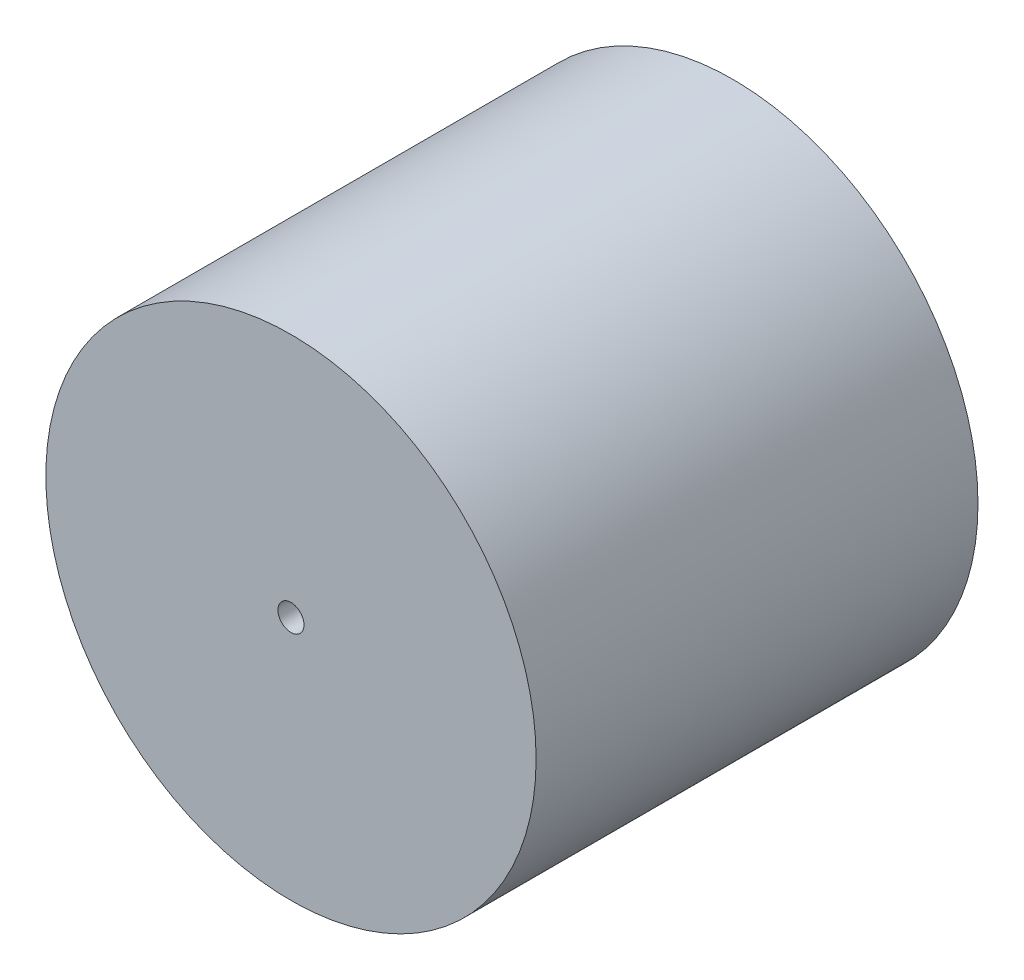
SolidWorks part; units mm, degrees
ref_plane "Front Plane" through (0, 0, 0) normal (0, 0, 1) x (1, 0, 0)
ref_plane "Top Plane" through (0, 0, 0) normal (0, 1, 0) x (1, 0, 0)
ref_plane "Right Plane" through (0, 0, 0) normal (1, 0, 0) x (0, 0, -1)
sketch "Sketch1" plane through (0, 0, 0) normal (0, 0, 1) x (1, 0, 0)
  circle A0 centre (0, 0) radius 38
  dimension "D1" = 76
extrude "Boss-Extrude1" add sketch "Sketch1" along normal blind 68.5
sketch "Sketch3" plane through (0, 0, 0) normal (0, 0, -1) x (-1, 0, 0)
  circle A0 centre (0, 0) radius 20.5
  dimension "D1" = 41
extrude "Cut-Extrude1" cut sketch "Sketch3" against normal blind 2
sketch "Sketch4" plane through (0, 0, 2) normal (0, 0, 1) x (1, 0, 0)
  circle A0 centre (0, 0) radius 11
  dimension "D1" = 22
extrude "Boss-Extrude3" add sketch "Sketch4" against normal blind 6.35
chamfer "Chamfer1" distance 4.35 angle 42 1 edges at (11, 0, -4.35)
sketch "Sketch5" plane through (0, 0, 68.5) normal (0, 0, 1) x (1, 0, 0)
  point P0 (0, 0)
hole_wizard "#10-32 Tapped Hole1" positions "3DSketch1" profile "Sketch6" tap size "#10-32" standard "ANSI Inch"
sketch3d "3DSketch1"
  point P0 (0, 0, 68.5)
sketch "Sketch6" plane through (0, 0, 68.5) normal (1, 0, 0) x (0, -1, 0)
  line L0 (0, 0) -> (0, 6.8133)
  line L1 (0, 6.8133) -> (2.0193, 5.6)
  line L2 (2.0193, 5.6) -> (2.0193, 0)
  line L5 (2.0193, 0) -> (0, 0)
  line L10 (0, 6.8133) -> (-2.0193, 5.6) construction
  line L11 (0, -6.35) -> (0, 107.95) construction
  dimension "Tap Drill Dia." = 4.0386
  dimension "Tap Drill Depth" = 5.6
  dimension "Drill Angle" = 118
cosmetic thread "Hole Thread2" parameters "D1"=9.652, "D2"=4.826
sketch "Sketch7" plane through (0, 0, -4.35) normal (0, 0, -1) x (-1, 0, 0)
  point P0 (0, 0)
hole_wizard "#10-32 Tapped Hole2" positions "3DSketch2" profile "Sketch8" tap size "#10-32" standard "ANSI Inch"
sketch3d "3DSketch2"
  point P0 (0, 0, -4.35)
sketch "Sketch8" plane through (0, 0, -4.35) normal (1, 0, 0) x (0, 1, 0)
  line L0 (0, 0) -> (0, 14.2133)
  line L1 (0, 14.2133) -> (2.0193, 13)
  line L2 (2.0193, 13) -> (2.0193, 0)
  line L5 (2.0193, 0) -> (0, 0)
  line L10 (0, 14.2133) -> (-2.0193, 13) construction
  line L11 (0, -6.35) -> (0, 107.95) construction
  dimension "Tap Drill Dia." = 4.0386
  dimension "Tap Drill Depth" = 13
  dimension "Drill Angle" = 118
cosmetic thread "Hole Thread3" parameters "D1"=9.652, "D2"=4.826
